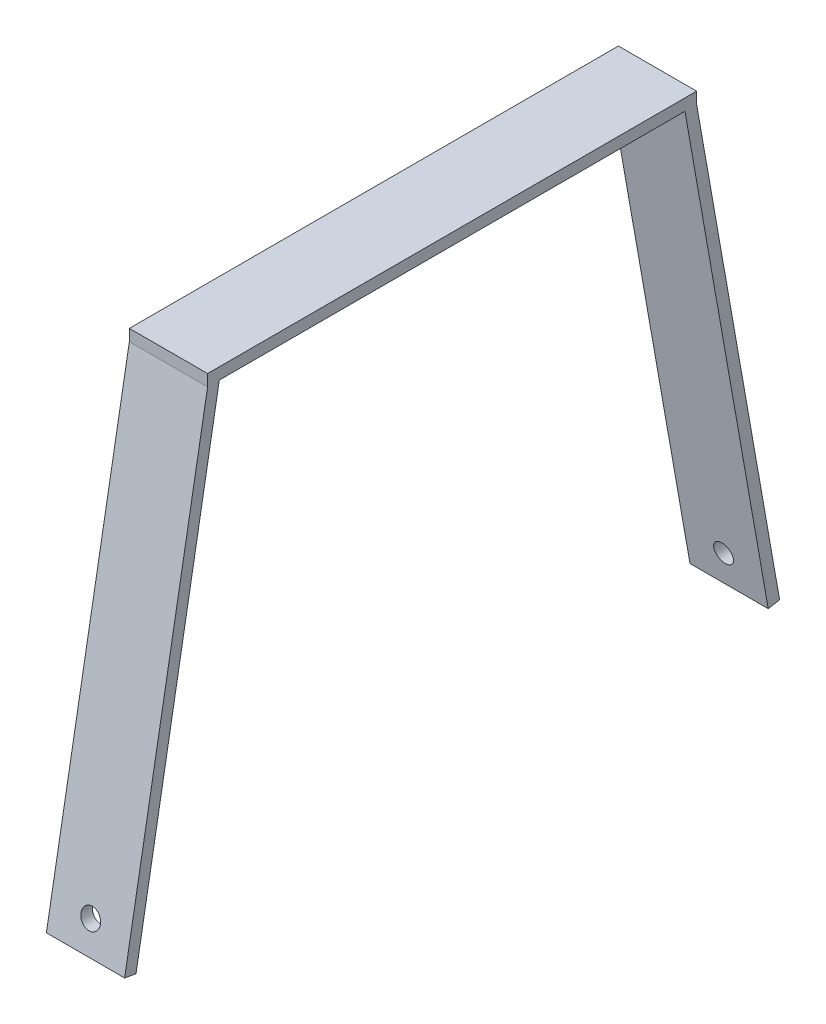
SolidWorks part; units mm, degrees
material "6063-T6"
ref_plane "Front Plane" through (0, 0, 0) normal (0, 0, 1) x (1, 0, 0)
ref_plane "Top Plane" through (0, 0, 0) normal (0, 1, 0) x (1, 0, 0)
ref_plane "Right Plane" through (0, 0, 0) normal (1, 0, 0) x (0, 0, -1)
sketch "Sketch2" plane through (0, 0, 0) normal (0, 1, 0) x (1, 0, 0)
  line L0 (-10.16, 63.5) -> (10.16, 63.5)
  line L1 (10.16, -63.5) -> (10.16, 63.5)
  line L2 (-10.16, -63.5) -> (-10.16, 63.5)
  line L3 (10.16, -63.5) -> (-10.16, -63.5)
  point P4 (0, 0)
extrude "Boss-Extrude1" add sketch "Sketch2" along normal blind 3
ref_plane "Plane1" through (0, 10.8591, 61.5852) normal (0, 0.1736, 0.9848) x (1, 0, 0)
sketch "Sketch4" plane through (0, 10.8591, 61.5852) normal (0, 0.1736, 0.9848) x (1, 0, 0)
  line L0 (-10.16, -8.0722) -> (10.16, -8.0722)
  line L1 (0, -8.0722) -> (0, -147.0794) construction
  line L2 (-10.16, -135.0722) -> (10.16, -135.0722)
  line L3 (10.16, -8.0722) -> (10.16, -135.0722)
  line L4 (-10.16, -135.0722) -> (-10.16, -8.0722)
  line L5 (0, -135.0722) -> (0, -124.9122)
  dimension "D2" = 10.16
  dimension "D1" = 127
extrude "Boss-Extrude2" add sketch "Sketch4" against normal blind 3
ref_plane "Plane3" through (0, 0, 85.09) normal (0, 0, 1) x (1, 0, 0)
sketch "Sketch6" plane through (0, 0, 85.09) normal (0, 0, 1) x (1, 0, 0)
  line L0 (0, -122.1611) -> (0, -114.5411)
  line L1 (-10.16, -122.1611) -> (10.16, -122.1611) construction
  circle A0 centre (0, -114.5411) radius 2.54
  dimension "D1" = 7.62
mirror "Mirror1" about plane through (0, 0, 0) normal (0, 0, 1) of "Boss-Extrude2"
extrude "Cut-Extrude2" cut sketch "Sketch6" against normal through all
